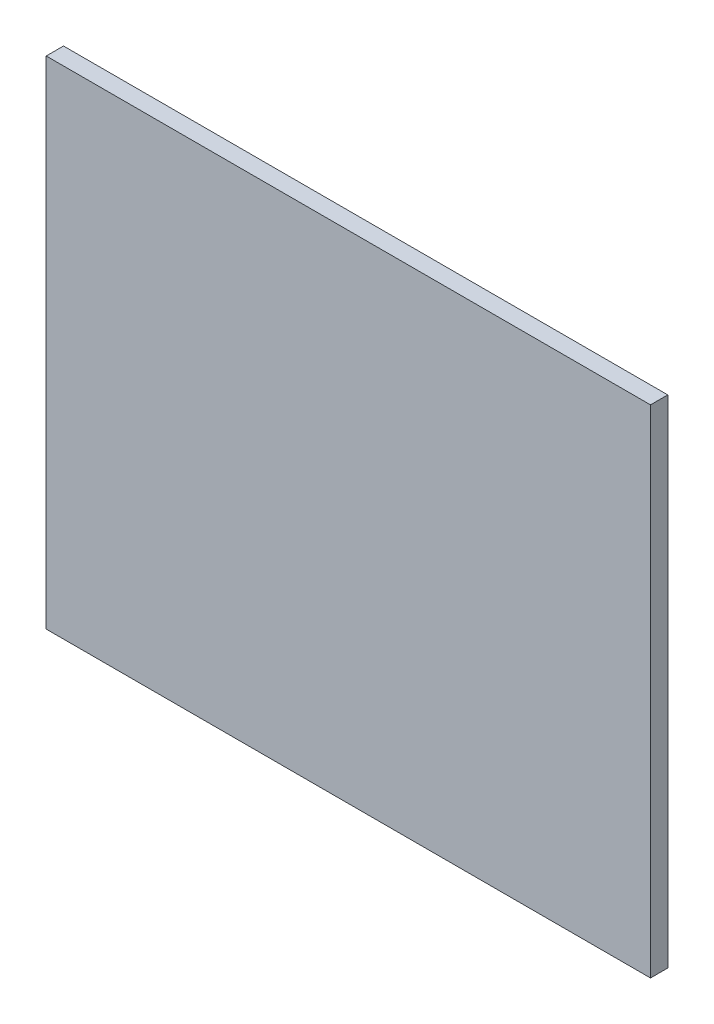
SolidWorks part; units mm, degrees
ref_plane "前视基准面" through (0, 0, 0) normal (0, 0, 1) x (1, 0, 0)
ref_plane "上视基准面" through (0, 0, 0) normal (0, 1, 0) x (1, 0, 0)
ref_plane "右视基准面" through (0, 0, 0) normal (1, 0, 0) x (0, 0, -1)
other "Configuration Table"
sketch "草图1" plane through (0, 0, 0) normal (0, 0, 1) x (1, 0, 0)
  line L1 (-63.5839, 46.0659) -> (76.4161, 46.0659)
  line L2 (-63.5839, 46.0659) -> (-63.5839, -68.9341)
  line L3 (-63.5839, -68.9341) -> (76.4161, -68.9341)
  line L4 (76.4161, 46.0659) -> (76.4161, -68.9341)
  dimension "D1" = 140
  dimension "D2" = 115
extrude "凸台-拉伸1" add sketch "草图1" along normal blind 4
